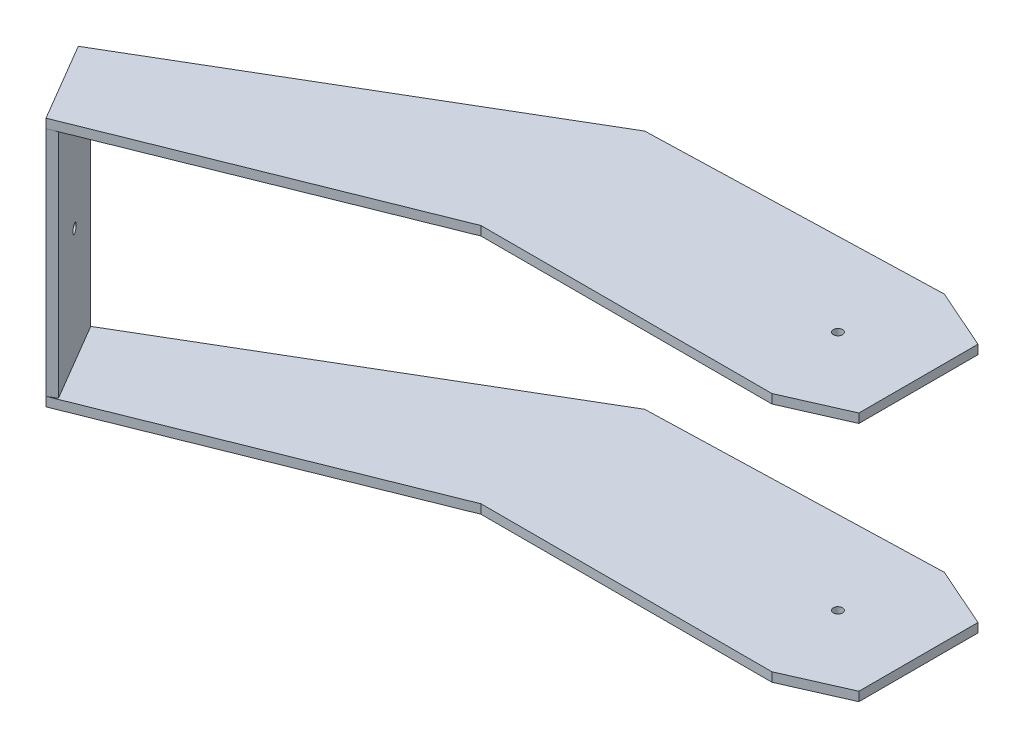
SolidWorks part; units mm, degrees
ref_plane "前视基准面" through (0, 0, 0) normal (0, 0, 1) x (1, 0, 0)
ref_plane "上视基准面" through (0, 0, 0) normal (0, 1, 0) x (1, 0, 0)
ref_plane "右视基准面" through (0, 0, 0) normal (1, 0, 0) x (0, 0, -1)
ref_plane "基准面7" through (0, 25.5, 0) normal (0, -1, 0) x (-1, 0, 0)
sketch "草图3" plane through (0, 25.5, 0) normal (0, -1, 0) x (-1, 0, 0)
  line L1 (0, 37.9064) -> (-13.2667, 32.0546)
  line L2 (0, 0) -> (-13.2667, 5.8519)
  line L3 (-13.2667, 32.0546) -> (-13.2667, 5.8519)
  line L4 (0, 0) -> (64, 0)
  line L6 (64, 36) -> (142.4348, -10.1408)
  line L7 (0, 37.9064) -> (64, 36)
  line L8 (132.294, -27.3793) -> (142.4348, -10.1408)
  line L9 (132.294, -27.3793) -> (64, 0)
extrude "凸台-拉伸3" add sketch "草图3" along normal blind 2 separate body
sketch "草图5" plane through (0, 25.5, 0) normal (0, -1, 0) x (-1, 0, 0)
  circle A0 centre (4.4333, 18.9532) radius 1
extrude "切除-拉伸3" cut sketch "草图5" along normal blind 2
sketch "草图6" plane through (-110.2479, 0, 64.8555) normal (-0.8619, 0, 0.507) x (0.507, 0, 0.8619)
  line L0 (-35.9071, 25.5) -> (35.9071, 25.5) construction
  line L1 (-63.4799, 25.5) -> (-43.4799, 25.5)
  line L2 (-63.4799, 25.5) -> (-63.4799, -29.5)
  line L3 (-63.4799, -29.5) -> (-43.4799, -29.5)
  line L4 (-43.4799, 25.5) -> (-43.4799, -29.5)
  line L5 (-63.4799, 23.5) -> (-63.4799, 25.5) construction
  point P8 (-43.4799, 25.5)
extrude "凸台-拉伸4" add sketch "草图6" against normal blind 2
sketch "草图8" plane through (0, -29.5, 0) normal (0, -1, 0) x (1, 0, 0)
  line L12 (0, 0) -> (-64, 0)
  line L15 (0, -37.9064) -> (13.2667, -32.0546)
  line L16 (13.2667, -32.0546) -> (13.2667, -5.8519)
  line L17 (0, 0) -> (13.2667, -5.8519)
  line L18 (-132.294, 27.3793) -> (-64, 0)
  line L19 (-132.294, 27.3793) -> (-142.4348, 10.1408)
  line L20 (-64, -36) -> (-142.4348, 10.1408)
  line L21 (0, -37.9064) -> (-64, -36)
extrude "凸台-拉伸5" add sketch "草图8" against normal blind 2
sketch "草图9" plane through (0, -29.5, 0) normal (0, -1, 0) x (1, 0, 0)
  circle A1 centre (-4.4333, -18.9532) radius 1
extrude "切除-拉伸4" cut sketch "草图9" against normal blind 2
sketch "草图10" plane through (-110.2479, 0, 64.8555) normal (-0.8619, 0, 0.507) x (0.507, 0, 0.8619)
  circle A0 centre (-53.4799, -2) radius 1
  point P0 (0, 0)
extrude "切除-拉伸5" cut sketch "草图10" against normal blind 2
